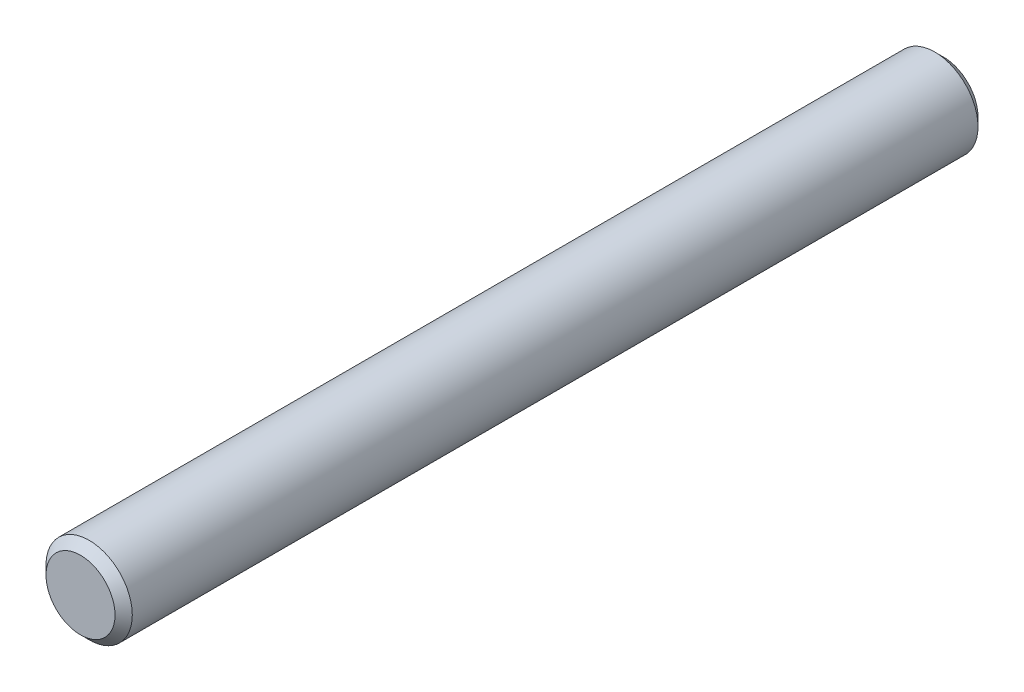
SolidWorks part; units mm, degrees
material "7075-T6 (SN)"
ref_plane "Front Plane" through (0, 0, 0) normal (0, 0, 1) x (1, 0, 0)
ref_plane "Top Plane" through (0, 0, 0) normal (0, 1, 0) x (1, 0, 0)
ref_plane "Right Plane" through (0, 0, 0) normal (1, 0, 0) x (0, 0, -1)
sketch "Sketch1" plane through (0, 0, 0) normal (0, 0, 1) x (1, 0, 0)
  circle A0 centre (0, 0) radius 5
  dimension "D1" = 10
extrude "Boss-Extrude1" add sketch "Sketch1" along normal blind 100
chamfer "Chamfer1" distance 1 angle 45 2 edges at (5, 0, 0) (5, 0, 100)
